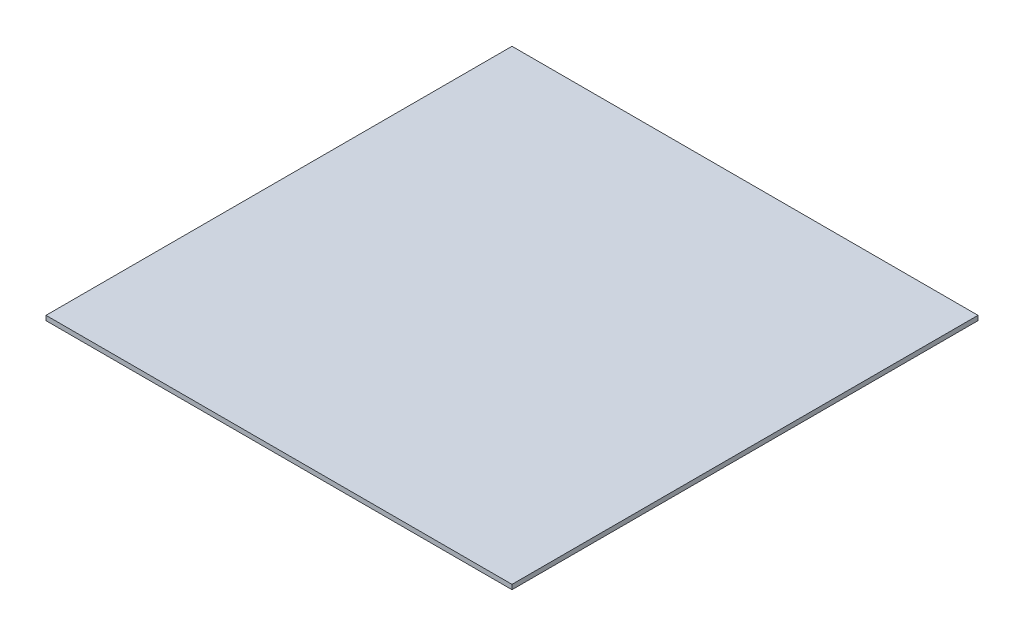
SolidWorks part; units mm, degrees
ref_plane "Front Plane" through (0, 0, 0) normal (0, 0, 1) x (1, 0, 0)
ref_plane "Top Plane" through (0, 0, 0) normal (0, 1, 0) x (1, 0, 0)
ref_plane "Right Plane" through (0, 0, 0) normal (1, 0, 0) x (0, 0, -1)
sketch "Sketch1" plane through (0, 0, 0) normal (0, 1, 0) x (1, 0, 0)
  line L1 (-50, -50) -> (50, -50)
  line L2 (-50, -50) -> (-50, 50)
  line L3 (-50, 50) -> (50, 50)
  line L4 (50, -50) -> (50, 50)
  line L5 (-50, -50) -> (50, 50) construction
  line L6 (-50, 50) -> (50, -50) construction
  point P0 (0, 0)
  dimension "D1" = 100
extrude "Boss-Extrude1" add sketch "Sketch1" along normal blind 1
